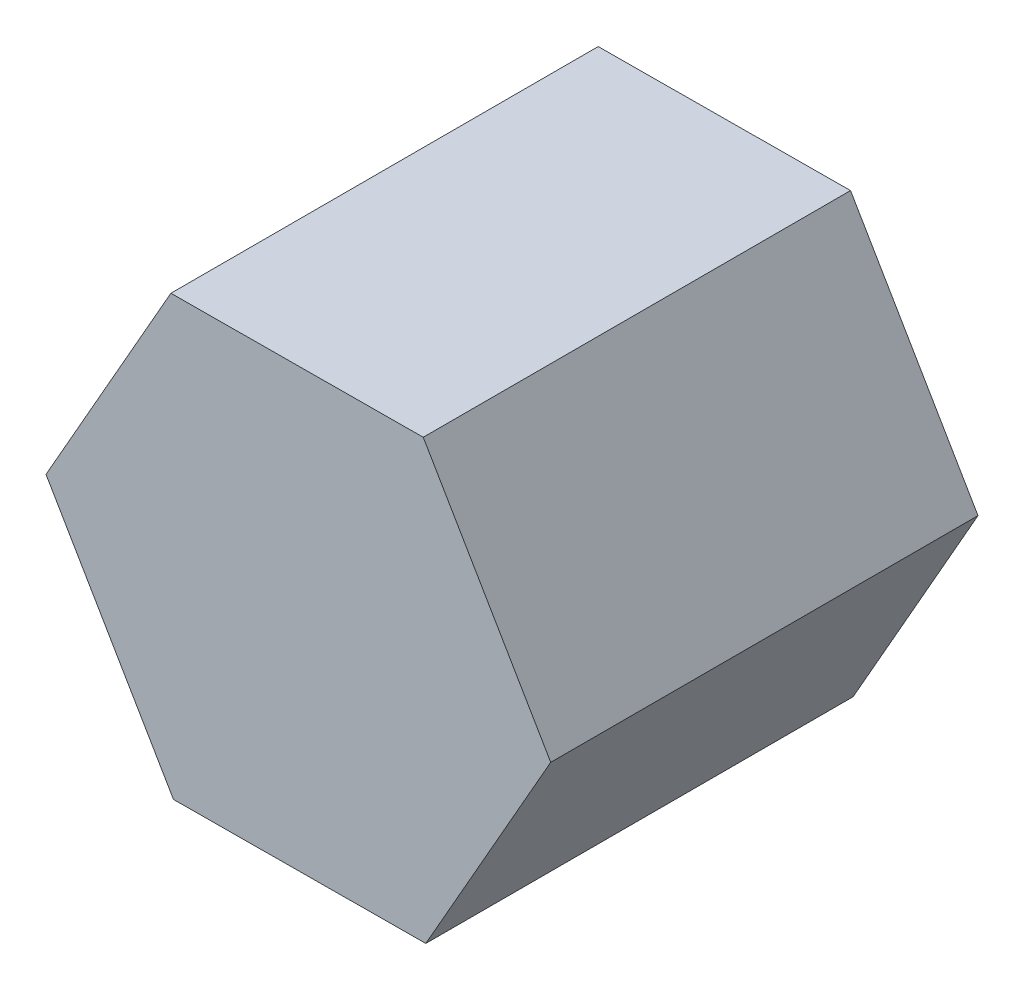
SolidWorks part; units mm, degrees
ref_plane "Piano frontale" through (0, 0, 0) normal (0, 0, 1) x (1, 0, 0)
ref_plane "Piano superiore" through (0, 0, 0) normal (0, 1, 0) x (1, 0, 0)
ref_plane "Piano destro" through (0, 0, 0) normal (1, 0, 0) x (0, 0, -1)
sketch "Schizzo1" plane through (0, 0, 0) normal (0, 0, 1) x (1, 0, 0)
  line L1 (-47.7285, 81.5613) -> (-94.4984, -0.5534)
  line L2 (-94.4984, -0.5534) -> (-46.7699, -82.1147)
  line L3 (-46.7699, -82.1147) -> (47.7285, -81.5613)
  line L4 (47.7285, -81.5613) -> (94.4984, 0.5534)
  line L5 (94.4984, 0.5534) -> (46.7699, 82.1147)
  line L6 (46.7699, 82.1147) -> (-47.7285, 81.5613)
  circle A0 centre (0, 0) radius 81.8394 construction
  dimension "D1" = 94.5
extrude "Estrusione-Estrusione1" add sketch "Schizzo1" along normal blind 160 contours L1 L2 L3 L4 L5 L6
